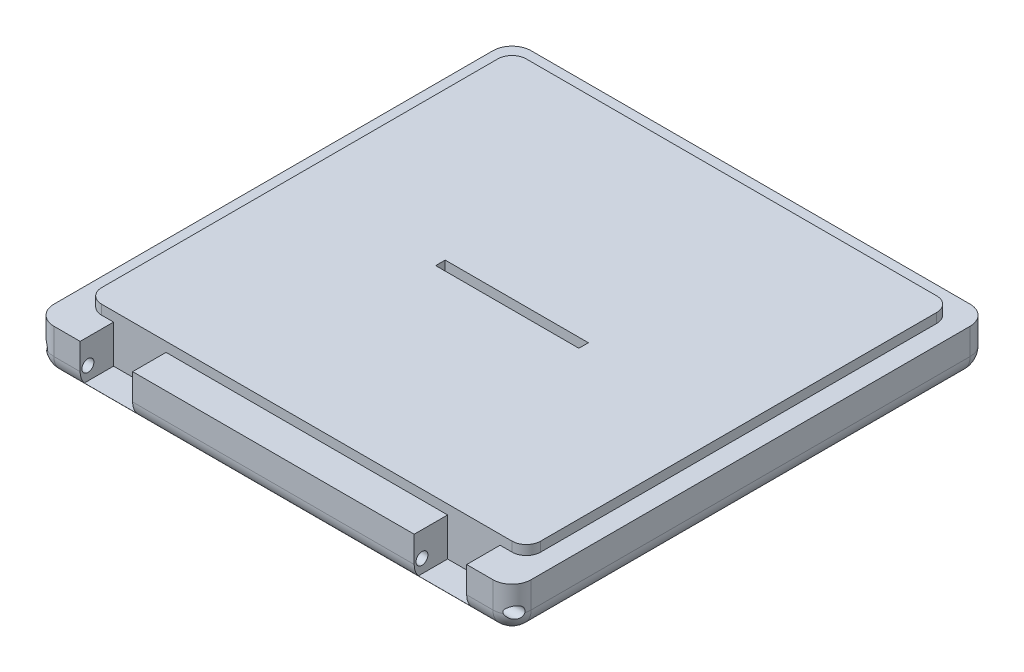
SolidWorks part; units mm, degrees
ref_plane "Спереди" through (0, 0, 0) normal (0, 0, 1) x (1, 0, 0)
ref_plane "Сверху" through (0, 0, 0) normal (0, 1, 0) x (1, 0, 0)
ref_plane "Справа" through (0, 0, 0) normal (1, 0, 0) x (0, 0, -1)
sketch "Эскиз1" plane through (0, 0, 0) normal (0, 1, 0) x (1, 0, 0)
  line L1 (-50, -50) -> (50, -50)
  line L2 (-50, -50) -> (-50, 50)
  line L3 (-50, 50) -> (50, 50)
  line L4 (50, -50) -> (50, 50)
  line L5 (-50, -50) -> (50, 50) construction
  line L6 (-50, 50) -> (50, -50) construction
  point P0 (0, 0)
  dimension "D1" = 100
  dimension "D2" = 100
extrude "Бобышка-Вытянуть1" add sketch "Эскиз1" along normal blind 9.5
fillet "Скругление1" radius 4 8 edges at (50, 4.75, 50) (50, 0, 0) (50, 4.75, -50) (0, 0, -50) (-50, 4.75, -50) (0, 0, 50) (-50, 0, 0) (-50, 4.75, 50)
sketch "Эскиз3" plane through (0, 9.5, 0) normal (0, 1, 0) x (1, 0, 0)
  line L1 (-46, -43) -> (46, -43)
  line L2 (-46, -43) -> (-46, 46)
  line L3 (-46, 46) -> (46, 46)
  line L4 (46, -43) -> (46, 46)
  line L5 (46, 50) -> (-46, 50) construction
  line L8 (-46, -50) -> (46, -50) construction
  line L9 (50, -46) -> (50, 46) construction
  line L10 (-50, 46) -> (-50, -46) construction
  point P0 (0, 0)
  dimension "D1" = 7
  dimension "D2" = 4
  dimension "D3" = 4
  dimension "D4" = 4
extrude "Бобышка-Вытянуть2" add sketch "Эскиз3" along normal blind 2
fillet "Скругление2" radius 3 4 edges at (46, 10.5, -46) (-46, 10.5, -46) (-46, 10.5, 43) (46, 10.5, 43)
sketch "Эскиз2" plane through (0, 9.5, 0) normal (0, 1, 0) x (1, 0, 0)
  line L0 (-46, -50) -> (46, -50) construction
  line L1 (40.5, -50) -> (29.5, -50)
  line L2 (40.5, -50) -> (40.5, -43)
  line L3 (40.5, -43) -> (29.5, -43)
  line L4 (29.5, -50) -> (29.5, -43)
  line L5 (50, -46) -> (50, 46) construction
  line L6 (-40.5, -50) -> (-29.5, -50)
  line L7 (-40.5, -50) -> (-40.5, -43)
  line L8 (-40.5, -43) -> (-29.5, -43)
  line L9 (-29.5, -50) -> (-29.5, -43)
  line L10 (-50, 46) -> (-50, -46) construction
  dimension "D1" = 9.5
  dimension "D2" = 11
  dimension "D3" = 9.5
  dimension "D4" = 11
  dimension "D5" = 7
  dimension "D6" = 7
extrude "Вырез-Вытянуть1" cut sketch "Эскиз2" against normal blind 8
sketch "Эскиз4" plane through (-40.5, 0, 0) normal (1, 0, 0) x (0, 0, -1)
  line L1 (-50, 4) -> (-50, 9.5) construction
  line L2 (-43, 1.5) -> (-49.1225, 1.5) construction
  circle A0 centre (-48.37, 4.3) radius 1.25
  point P2 (-48.37, 3.05)
  point P4 (-49.62, 4.3)
  dimension "D1" = 2.5
  dimension "D2" = 0.38
  dimension "D3" = 1.55
extrude "Вырез-Вытянуть2" cut sketch "Эскиз4" against normal through all and the other way through all
sketch "Эскиз5" plane through (0, 0, 0) normal (0, -1, 0) x (1, 0, 0)
  line L1 (-15, -1) -> (15, -1)
  line L2 (-15, -1) -> (-15, 1)
  line L3 (-15, 1) -> (15, 1)
  line L4 (15, -1) -> (15, 1)
  line L5 (-15, -1) -> (15, 1) construction
  line L6 (-15, 1) -> (15, -1) construction
  point P0 (0, 0)
  dimension "D1" = 2
  dimension "D2" = 30
extrude "Вырез-Вытянуть3" cut sketch "Эскиз5" against normal through all
